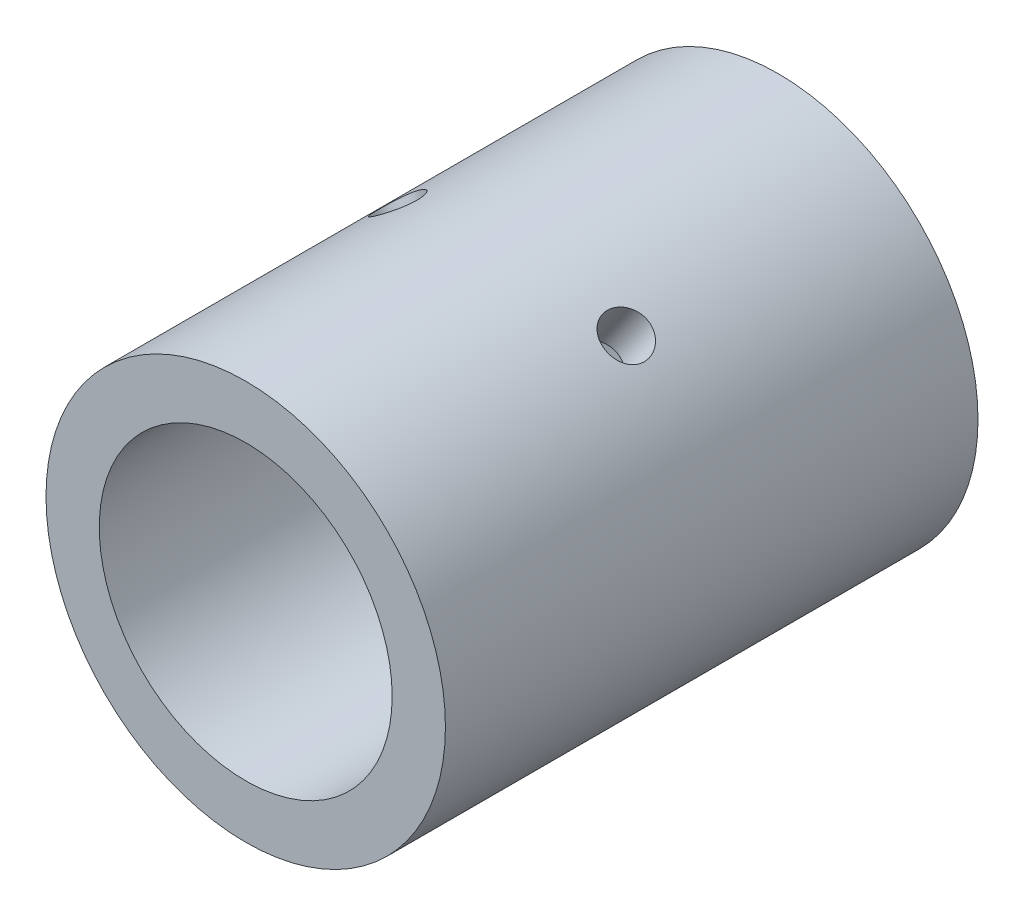
SolidWorks part; units mm, degrees
ref_plane "Front Plane" through (0, 0, 0) normal (0, 0, 1) x (1, 0, 0)
ref_plane "Top Plane" through (0, 0, 0) normal (0, 1, 0) x (1, 0, 0)
ref_plane "Right Plane" through (0, 0, 0) normal (1, 0, 0) x (0, 0, -1)
sketch "Skica1" plane through (0, 0, 0) normal (0, 0, 1) x (1, 0, 0)
  circle A0 centre (0, 0) radius 37.5
  dimension "D1" = 75
extrude "Vysunout tenkostěnný1" add sketch "Skica1" along normal mid plane 100 thin thin type one direction reverse wall 10
sketch "Skica2" plane through (0, 0, 0) normal (0, 0, 1) x (1, 0, 0)
  line L0 (0, 0) -> (-21.5091, 30.7182) construction
  line L1 (-21.5091, 30.7182) -> (21.5091, 30.7182) construction
  line L2 (21.5091, 30.7182) -> (0, 0) construction
  circle A0 centre (0, 0) radius 37.5 construction
  dimension "D1" = 70
hole_wizard "M10 závit1" positions "3DSkica1" profile "Skica3" tap size "M10" standard "ISO"
sketch3d "3DSkica1"
  point P12 (-21.5091, 30.7182, 0)
  point P14 (21.5091, 30.7182, 0)
  point P17 (0, 0, 0)
  point P18 (-21.5091, 30.7182, 0)
  point P20 (21.5091, 30.7182, 0)
sketch "Skica3" plane through (-21.5091, 30.7182, 0) normal (0, 0, 1) x (-0.8192, -0.5736, 0)
  line L0 (0, 0) -> (0, 30.0537)
  line L1 (0, 30.0537) -> (4.25, 27.5)
  line L2 (4.25, 27.5) -> (4.25, 0)
  line L5 (4.25, 0) -> (0, 0)
  line L10 (0, 30.0537) -> (-4.25, 27.5) construction
  line L11 (0, -6.35) -> (0, 107.95) construction
  dimension "Průměr závitníku" = 8.5
  dimension "Hloubka závitníku" = 27.5
  dimension "Úhel vrtání" = 118
cosmetic thread "Závit díry1" parameters "D1"=10.3304, "D2"=10
cosmetic thread "Závit díry2" parameters "D1"=10.3304, "D2"=10
